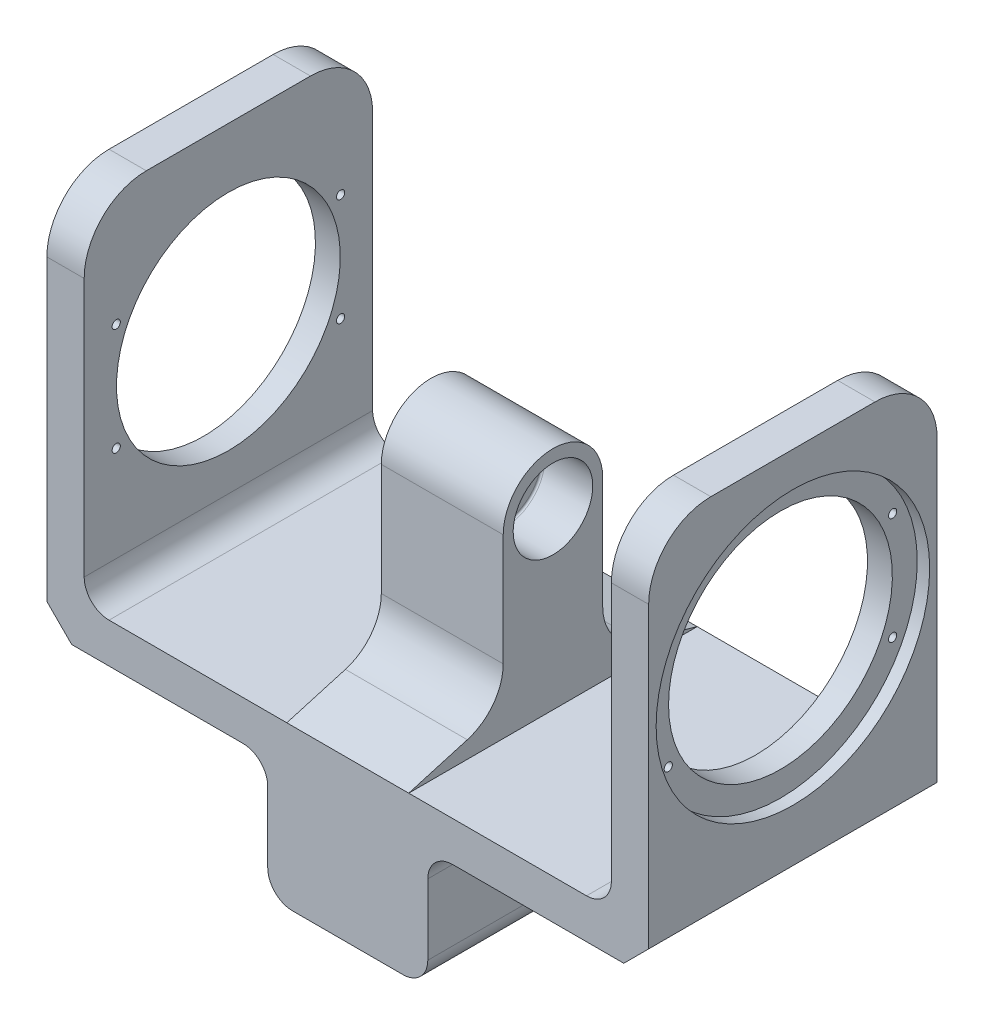
SolidWorks part; units mm, degrees
material "1060 Alloy"
ref_plane "Front Plane" through (0, 0, 0) normal (0, 0, 1) x (1, 0, 0)
ref_plane "Top Plane" through (0, 0, 0) normal (0, 1, 0) x (1, 0, 0)
ref_plane "Right Plane" through (0, 0, 0) normal (1, 0, 0) x (0, 0, -1)
sketch "Sketch1" plane through (0, 0, 0) normal (0, 0, 1) x (1, 0, 0)
  line L0 (0, 0) -> (-106, 0)
  line L1 (55, 0) -> (-55, 0) construction
  line L3 (-121, 0) -> (-121, 155)
  line L4 (-121, 155) -> (-106, 155)
  line L5 (-106, 155) -> (-106, 16)
  line L7 (-106, 16) -> (-24.51, 16)
  line L9 (-24.51, 16) -> (-24.51, 107)
  line L10 (-24.51, 107) -> (0, 107)
  line L11 (0, -55) -> (0, 55) construction
  line L12 (0, 107) -> (0, 0)
  line L13 (-121, 0) -> (-106, 0)
  dimension "D1" = 24.51
  dimension "D2" = 91
  dimension "D4" = 121
  dimension "D5" = 15
  dimension "D6" = 16
  dimension "D8" = 48
extrude "Boss-Extrude1" add sketch "Sketch1" against normal blind 116
sketch "Sketch5" plane through (-24.51, 0, 0) normal (-1, 0, 0) x (0, 0, 1)
  line L0 (-116, 107) -> (0, 107) construction
  line L1 (0, 107) -> (0, 16) construction
  circle A0 centre (-58, 86) radius 16
  dimension "D3" = 32
  dimension "D1" = 21
  dimension "D2" = 58
extrude "Cut-Extrude1" cut sketch "Sketch5" against normal blind 20
sketch "Sketch6" plane through (-4.51, 0, 0) normal (-1, 0, 0) x (0, 0, 1)
  circle A0 centre (-58, 86) radius 10
  dimension "D1" = 20
extrude "Cut-Extrude2" cut sketch "Sketch6" against normal up to next
sketch "Sketch8" plane through (-106, 0, 0) normal (1, 0, 0) x (0, 0, -1)
  circle A0 centre (58, 86) radius 45
  circle A1 centre (58, 86) radius 10 construction
  dimension "D1" = 90
extrude "Cut-Extrude4" cut sketch "Sketch8" against normal up to next
sketch "Sketch10" plane through (0, 0, 0) normal (1, 0, 0) x (0, 0, -1)
  line L1 (0, 66.55) -> (0, -66.55) construction
  line L2 (116, 0) -> (116, 107) construction
  line L5 (0, 16) -> (0, 107)
  line L6 (116, 107) -> (0, 107) construction
  line L7 (0, 107) -> (116, 107)
  line L8 (116, 107) -> (116, 16)
  line L9 (38, 87) -> (38, 42.0316)
  line L11 (25, 16) -> (57, 16)
  line L13 (116, 0) -> (0, 0) construction
  line L14 (25, 16) -> (0, 16)
  line L15 (0, 107) -> (116, 107)
  line L16 (116, 16) -> (57, 16)
  line L17 (23.5612, 22.8203) -> (0, 16)
  line L18 (78, 87) -> (78, 42.0316)
  line L19 (92.4388, 22.8203) -> (116, 16)
  arc A0 (38, 87) -> (78, 87) centre (58, 87) cw
  arc A1 (78, 42.0316) -> (92.4388, 22.8203) centre (98, 42.0316) ccw
  arc A2 (38, 42.0316) -> (23.5612, 22.8203) centre (18, 42.0316) cw
  point P18 (58, 107)
  point P23 (78, 27)
  point P27 (38, 27)
  dimension "D2" = 20
  dimension "D3" = 60
  dimension "D4" = 20
  dimension "D1" = 16
extrude "Cut-Extrude5" cut sketch "Sketch10" against normal up to surface (106 mm away)
fillet "Fillet3" radius 25 2 edges at (-113.5, 155, -116) (-113.5, 155, 0)
sketch "Sketch21" plane through (-121, 0, 0) normal (-1, 0, 0) x (0, 0, 1)
  circle A0 centre (-58, 86) radius 55
  circle A1 centre (-58, 86) radius 45 construction
  dimension "D1" = 10
extrude "Cut-Extrude7" cut sketch "Sketch21" against normal blind 5
hole_wizard "M4x0.7 Tapped Hole1" positions "Sketch22" profile "Sketch23" tap size "M4x0.7" standard "ANSI Metric"
sketch "Sketch22" plane through (-116, 0, 0) normal (-1, 0, 0) x (0, 0, 1)
  circle A0 centre (-58, 86) radius 50
  point P0 (-103.1086, 107.5689)
  point P2 (-12.8914, 107.5689)
  point P4 (-12.8914, 64.4311)
  point P6 (-103.1086, 64.4311)
  dimension "D1" = 100
sketch "Sketch23" plane through (-116, 107.5689, -103.1086) normal (0, 1, 0) x (0, 0, 1)
  line L0 (0, 0) -> (0, 10.9904)
  line L1 (0, 10.9904) -> (1.65, 9.999)
  line L2 (1.65, 9.999) -> (1.65, 0)
  line L5 (1.65, 0) -> (0, 0)
  line L10 (0, 10.9904) -> (-1.65, 9.999) construction
  line L11 (0, -6.35) -> (0, 107.95) construction
  dimension "Tap Drill Dia." = 3.3
  dimension "Tap Drill Depth" = 9.999
  dimension "Drill Angle" = 118
mirror "Mirror1" about plane through (0, 107, -116) normal (1, 0, 0) of bodies 128
fillet "Fillet4" radius 0.8 2 edges at (4.51, 70, -58) (-4.51, 70, -58)
chamfer "Chamfer1" distance 10 angle 45 2 edges at (-121, 0, -58) (121, 0, -58)
sketch "Sketch25" plane through (0, 0, 0) normal (0, 0, 1) x (1, 0, 0)
  line L0 (-111, 0) -> (111, 0) construction
  line L1 (32.178, 0) -> (-32.178, 0)
  line L2 (32.178, 0) -> (32.178, -48.356)
  line L3 (32.178, -48.356) -> (-32.178, -48.356)
  line L4 (-32.178, 0) -> (-32.178, -48.356)
  line L5 (-24.51, 16) -> (24.51, 16) construction
  point P6 (0, 0)
  dimension "D1" = 64.356
  dimension "D2" = 64.356
extrude "Boss-Extrude2" add sketch "Sketch25" against normal up to surface (116 mm away) up to face at (0, 50.3333, -116)
sketch "Sketch27" plane through (0, 0, -116) normal (0, 0, -1) x (-1, 0, 0)
  line L0 (32.178, -48.356) -> (-32.178, -48.356) construction
  line L1 (-21.0503, -43.356) -> (21.0502, -43.356)
  line L2 (-27.178, -37.2283) -> (-27.178, 4.8722)
  line L3 (-21.0503, 11) -> (21.0502, 11)
  line L4 (27.178, -37.2283) -> (27.178, 4.8722)
  line L5 (-27.178, -43.356) -> (27.178, 11) construction
  line L6 (-27.178, 11) -> (27.178, -43.356) construction
  arc A0 (-21.0503, -43.356) -> (-27.178, -37.2283) centre (-21.0503, -37.2283) cw
  arc A1 (21.0502, -43.356) -> (27.178, -37.2283) centre (21.0502, -37.2283) ccw
  arc A2 (21.0502, 11) -> (27.178, 4.8722) centre (21.0502, 4.8722) cw
  arc A3 (-27.178, 4.8722) -> (-21.0503, 11) centre (-21.0503, 4.8722) cw
  point P0 (0, -16.178)
  dimension "D4" = 6.1277
  dimension "D1" = 32.178
  dimension "D2" = 54.356
  dimension "D3" = 54.356
extrude "Cut-Extrude8" cut sketch "Sketch27" against normal offset from surface (106 mm away) 10 up to face at (0, 31.7055, 0)
fillet "Fillet6" radius 10 2 edges at (32.178, 0, -58) (-32.178, 0, -58)
fillet "Fillet7" radius 10 2 edges at (32.178, -48.356, -58) (-32.178, -48.356, -58)
fillet "Fillet8" radius 10 2 edges at (106, 16, -58) (-106, 16, -58)
